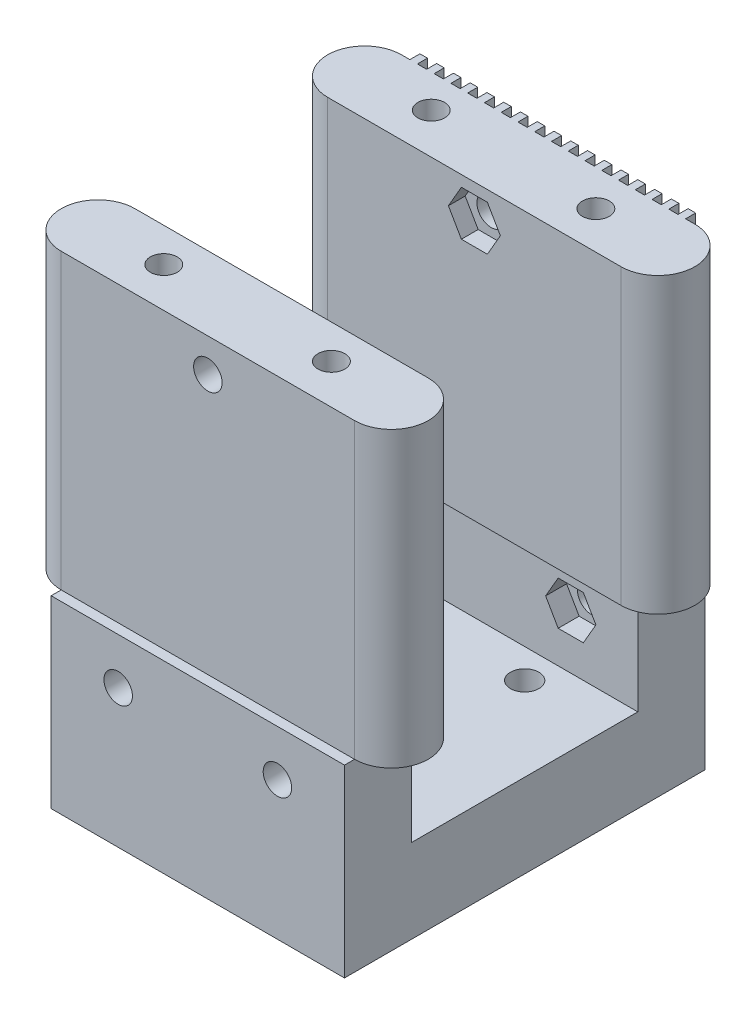
SolidWorks part; units mm, degrees
ref_plane "Front Plane" through (0, 0, 0) normal (0, 0, 1) x (1, 0, 0)
ref_plane "Top Plane" through (0, 0, 0) normal (0, 1, 0) x (1, 0, 0)
ref_plane "Right Plane" through (0, 0, 0) normal (1, 0, 0) x (0, 0, -1)
sketch "Sketch11" plane through (0, 0, 12.5) normal (0, -1, 0) x (1, 0, 0)
  line L1 (0, 0) -> (35, 0)
  line L2 (0, 0) -> (0, -27)
  line L3 (0, -27) -> (35, -27)
  line L4 (35, 0) -> (35, -27)
  dimension "D1" = 27
  dimension "D2" = 35
extrude "Boss-Extrude6" add sketch "Sketch11" along normal blind 10
sketch "Sketch12" plane through (0, -10, 0) normal (0, -1, 0) x (1, 0, 0)
  line L0 (0, 12.5) -> (0, -14.5) construction
  line L1 (0, -14.5) -> (35, -14.5) construction
  line L3 (35, 12.5) -> (0, 12.5) construction
  circle A0 centre (10, 9) radius 1.7
  circle A1 centre (25, 9) radius 1.7
  circle A2 centre (25, -11) radius 1.7
  circle A3 centre (10, -11) radius 1.7
  point P0 (17.5, -1)
  dimension "D3" = 3.4
  dimension "D4" = 7.5
  dimension "D1" = 17.5
  dimension "D2" = 13.5
  dimension "D5" = 10
  dimension "D7" = 27
  dimension "D6" = 2
extrude "Cut-Extrude3" cut sketch "Sketch12" against normal through all
sketch "Sketch13" plane through (0, -10, 0) normal (0, -1, 0) x (1, 0, 0)
  line L1 (35, -14.5) -> (0, -14.5)
  line L2 (35, -14.5) -> (35, -22.5)
  line L3 (35, -22.5) -> (0, -22.5)
  line L4 (0, -14.5) -> (0, -22.5)
  line L5 (35, 12.5) -> (0, 12.5)
  line L6 (35, 12.5) -> (35, 20.5)
  line L7 (35, 20.5) -> (0, 20.5)
  line L8 (0, 12.5) -> (0, 20.5)
  dimension "D1" = 8
  dimension "D2" = 8
extrude "Boss-Extrude7" add sketch "Sketch13" against normal blind 22
sketch "Sketch14" plane through (0, 12, 0) normal (0, 1, 0) x (1, 0, 0)
  line L0 (0, -12.5) -> (35, -12.5) construction
  line L1 (35, -20.5) -> (0, -20.5)
  line L2 (35, -20.5) -> (35, -10.5)
  line L3 (35, -10.5) -> (0, -10.5)
  line L4 (0, -20.5) -> (0, -10.5)
  line L5 (0, 22.5) -> (35, 22.5)
  line L6 (0, 22.5) -> (0, 12.5)
  line L7 (0, 12.5) -> (35, 12.5)
  line L8 (35, 22.5) -> (35, 12.5)
  line L9 (35, 14.5) -> (0, 14.5) construction
  dimension "D1" = 2
  dimension "D2" = 2
extrude "Boss-Extrude8" add sketch "Sketch14" along normal blind 35
sketch "Sketch17" plane through (0, 0, 20.5) normal (0, 0, 1) x (1, 0, 0)
  line L1 (0, 47) -> (35, 47)
  line L2 (0, 47) -> (0, 12)
  line L3 (0, 12) -> (35, 12)
  line L4 (35, 47) -> (35, 12)
  line L5 (35, 47) -> (35, -10) construction
  dimension "D1" = 35
extrude "Cut-Extrude6" cut sketch "Sketch17" against normal blind 1.2
sketch "Sketch18" plane through (0, 0, -22.5) normal (0, 0, -1) x (-1, 0, 0)
  line L0 (-31.9, 47) -> (-31.9, 12)
  line L1 (-35, 47) -> (-33.9, 47)
  line L2 (-35, 47) -> (-35, 12)
  line L3 (-35, 12) -> (-33.9, 12)
  line L4 (-33.9, 47) -> (-33.9, 12)
  line L5 (-33, 12) -> (-31.9, 12)
  line L6 (-33, 47) -> (-33, 12)
  line L7 (-33, 47) -> (-31.9, 47)
  line L8 (-29.9, 47) -> (-29.9, 12)
  line L9 (-31, 12) -> (-29.9, 12)
  line L10 (-31, 47) -> (-31, 12)
  line L11 (-31, 47) -> (-29.9, 47)
  line L12 (-27.9, 47) -> (-27.9, 12)
  line L13 (-29, 12) -> (-27.9, 12)
  line L14 (-29, 47) -> (-29, 12)
  line L15 (-29, 47) -> (-27.9, 47)
  line L16 (-25.9, 47) -> (-25.9, 12)
  line L17 (-27, 12) -> (-25.9, 12)
  line L18 (-27, 47) -> (-27, 12)
  line L19 (-27, 47) -> (-25.9, 47)
  line L20 (-23.9, 47) -> (-23.9, 12)
  line L21 (-25, 12) -> (-23.9, 12)
  line L22 (-25, 47) -> (-25, 12)
  line L23 (-25, 47) -> (-23.9, 47)
  line L24 (-21.9, 47) -> (-21.9, 12)
  line L25 (-23, 12) -> (-21.9, 12)
  line L26 (-23, 47) -> (-23, 12)
  line L27 (-23, 47) -> (-21.9, 47)
  line L28 (-19.9, 47) -> (-19.9, 12)
  line L29 (-21, 12) -> (-19.9, 12)
  line L30 (-21, 47) -> (-21, 12)
  line L31 (-21, 47) -> (-19.9, 47)
  line L32 (-17.9, 47) -> (-17.9, 12)
  line L33 (-19, 12) -> (-17.9, 12)
  line L34 (-19, 47) -> (-19, 12)
  line L35 (-19, 47) -> (-17.9, 47)
  line L36 (-15.9, 47) -> (-15.9, 12)
  line L37 (-17, 12) -> (-15.9, 12)
  line L38 (-17, 47) -> (-17, 12)
  line L39 (-17, 47) -> (-15.9, 47)
  line L40 (-13.9, 47) -> (-13.9, 12)
  line L41 (-15, 12) -> (-13.9, 12)
  line L42 (-15, 47) -> (-15, 12)
  line L43 (-15, 47) -> (-13.9, 47)
  line L44 (-11.9, 47) -> (-11.9, 12)
  line L45 (-13, 12) -> (-11.9, 12)
  line L46 (-13, 47) -> (-13, 12)
  line L47 (-13, 47) -> (-11.9, 47)
  line L48 (-9.9, 47) -> (-9.9, 12)
  line L49 (-11, 12) -> (-9.9, 12)
  line L50 (-11, 47) -> (-11, 12)
  line L51 (-11, 47) -> (-9.9, 47)
  line L52 (-7.9, 47) -> (-7.9, 12)
  line L53 (-9, 12) -> (-7.9, 12)
  line L54 (-9, 47) -> (-9, 12)
  line L55 (-9, 47) -> (-7.9, 47)
  line L56 (-5.9, 47) -> (-5.9, 12)
  line L57 (-7, 12) -> (-5.9, 12)
  line L58 (-7, 47) -> (-7, 12)
  line L59 (-7, 47) -> (-5.9, 47)
  line L60 (-3.9, 47) -> (-3.9, 12)
  line L61 (-5, 12) -> (-3.9, 12)
  line L62 (-5, 47) -> (-5, 12)
  line L63 (-5, 47) -> (-3.9, 47)
  line L64 (-1.9, 47) -> (-1.9, 12)
  line L65 (-3, 12) -> (-1.9, 12)
  line L66 (-3, 47) -> (-3, 12)
  line L67 (-3, 47) -> (-1.9, 47)
  line L68 (0.1, 47) -> (0.1, 12)
  line L69 (-1, 12) -> (0.1, 12)
  line L70 (-1, 47) -> (-1, 12)
  line L71 (-1, 47) -> (0.1, 47)
  dimension "D1" = 1.1
  dimension "D2" = 35
  dimension "D3" = 18
extrude "Cut-Extrude7" cut sketch "Sketch18" against normal blind 1.2
sketch "Sketch19" plane through (0, 0, -22.5) normal (0, 0, -1) x (-1, 0, 0)
  line L0 (-35, 12) -> (-35, -10) construction
  line L1 (0, 12) -> (0, -10) construction
  line L2 (-13.9, 47) -> (-13, 47) construction
  circle A0 centre (-27, 6.4851) radius 1.7
  circle A1 centre (-8, 6.4851) radius 1.7
  circle A2 centre (-17.5, 43) radius 1.7
  dimension "D1" = 8
  dimension "D3" = 3.4
  dimension "D4" = 3.4
  dimension "D5" = 17.5
  dimension "D2" = 8
  dimension "D6" = 4
extrude "Cut-Extrude8" cut sketch "Sketch19" against normal through all
sketch "Sketch20" plane through (0, 0, -14.5) normal (0, 0, 1) x (1, 0, 0)
  line L1 (28.5, 3.887) -> (30, 6.4851)
  line L2 (30, 6.4851) -> (28.5, 9.0832)
  line L3 (28.5, 9.0832) -> (25.5, 9.0832)
  line L4 (25.5, 9.0832) -> (24, 6.4851)
  line L5 (24, 6.4851) -> (25.5, 3.887)
  line L6 (25.5, 3.887) -> (28.5, 3.887)
  line L7 (9.5, 3.887) -> (11, 6.4851)
  line L8 (11, 6.4851) -> (9.5, 9.0832)
  line L9 (9.5, 9.0832) -> (6.5, 9.0832)
  line L10 (6.5, 9.0832) -> (5, 6.4851)
  line L11 (5, 6.4851) -> (6.5, 3.887)
  line L12 (6.5, 3.887) -> (9.5, 3.887)
  circle A0 centre (27, 6.4851) radius 2.5981 construction
  circle A1 centre (8, 6.4851) radius 2.5981 construction
  dimension "D1" = 3
  dimension "D2" = 3
extrude "Cut-Extrude9" cut sketch "Sketch20" against normal blind 2.5
sketch "Sketch21" plane through (0, 0, 12.5) normal (0, 0, -1) x (-1, 0, 0)
  line L1 (-6.45, 3.8004) -> (-4.9, 6.4851)
  line L2 (-4.9, 6.4851) -> (-6.45, 9.1698)
  line L3 (-6.45, 9.1698) -> (-9.55, 9.1698)
  line L4 (-9.55, 9.1698) -> (-11.1, 6.4851)
  line L5 (-11.1, 6.4851) -> (-9.55, 3.8004)
  line L6 (-9.55, 3.8004) -> (-6.45, 3.8004)
  line L7 (-25.45, 3.8004) -> (-23.9, 6.4851)
  line L8 (-23.9, 6.4851) -> (-25.45, 9.1698)
  line L9 (-25.45, 9.1698) -> (-28.55, 9.1698)
  line L10 (-28.55, 9.1698) -> (-30.1, 6.4851)
  line L11 (-30.1, 6.4851) -> (-28.55, 3.8004)
  line L12 (-28.55, 3.8004) -> (-25.45, 3.8004)
  circle A0 centre (-8, 6.4851) radius 2.6847 construction
  circle A1 centre (-27, 6.4851) radius 2.6847 construction
  dimension "D1" = 3.1
  dimension "D2" = 3.1
extrude "Cut-Extrude10" cut sketch "Sketch21" against normal blind 2.5
sketch "Sketch22" plane through (0, 47, 0) normal (0, 1, 0) x (1, 0, 0)
  line L0 (35, -19.3) -> (35, -10.5) construction
  line L1 (0, -10.5) -> (0, -19.3) construction
  line L2 (35, 21.3) -> (35, 12.5)
  line L3 (35, -10.5) -> (35, -19.3)
  line L4 (0, 21.3) -> (0, 12.5)
  line L5 (0, -10.5) -> (0, -19.3)
  arc A0 (35, 21.3) -> (35, 12.5) centre (35, 16.9) cw
  arc A1 (35, -10.5) -> (35, -19.3) centre (35, -14.9) cw
  arc A2 (0, 12.5) -> (0, 21.3) centre (0, 16.9) cw
  arc A3 (0, -10.5) -> (0, -19.3) centre (0, -14.9) ccw
extrude "Boss-Extrude9" add sketch "Sketch22" against normal blind 35
sketch "Sketch23" plane through (0, 47, 0) normal (0, 1, 0) x (1, 0, 0)
  line L0 (0, 21.3) -> (0, 12.5) construction
  line L1 (35, 12.5) -> (35, 21.3) construction
  circle A0 centre (7.5, 17.3527) radius 1.6
  circle A1 centre (27.5, 16.995) radius 1.6
  circle A2 centre (27.5, -14.5597) radius 1.6
  circle A3 centre (7.5, -14.5597) radius 1.6
  arc A4 (0, 21.3) -> (0, 12.5) centre (0, 16.9) ccw construction
  arc A5 (35, 12.5) -> (35, 21.3) centre (35, 16.9) ccw construction
  dimension "D1" = 3.2
  dimension "D2" = 20
  dimension "D3" = 20
  dimension "D4" = 7.5
  dimension "D5" = 7.5
extrude "Cut-Extrude11" cut sketch "Sketch23" against normal blind 15
sketch "Sketch24" plane through (0, 0, 10.5) normal (0, 0, -1) x (-1, 0, 0)
  line L1 (-15.95, 40.3153) -> (-14.4, 43)
  line L2 (-14.4, 43) -> (-15.95, 45.6847)
  line L3 (-15.95, 45.6847) -> (-19.05, 45.6847)
  line L4 (-19.05, 45.6847) -> (-20.6, 43)
  line L5 (-20.6, 43) -> (-19.05, 40.3153)
  line L6 (-19.05, 40.3153) -> (-15.95, 40.3153)
  circle A0 centre (-17.5, 43) radius 2.6847 construction
  dimension "D1" = 3.1
extrude "Cut-Extrude12" cut sketch "Sketch24" against normal blind 2
sketch "Sketch25" plane through (0, 0, -12.5) normal (0, 0, 1) x (1, 0, 0)
  line L1 (19.05, 40.3153) -> (20.6, 43)
  line L2 (20.6, 43) -> (19.05, 45.6847)
  line L3 (19.05, 45.6847) -> (15.95, 45.6847)
  line L4 (15.95, 45.6847) -> (14.4, 43)
  line L5 (14.4, 43) -> (15.95, 40.3153)
  line L6 (15.95, 40.3153) -> (19.05, 40.3153)
  circle A0 centre (17.5, 43) radius 2.6847 construction
  dimension "D1" = 3.1
extrude "Cut-Extrude13" cut sketch "Sketch25" against normal blind 2
